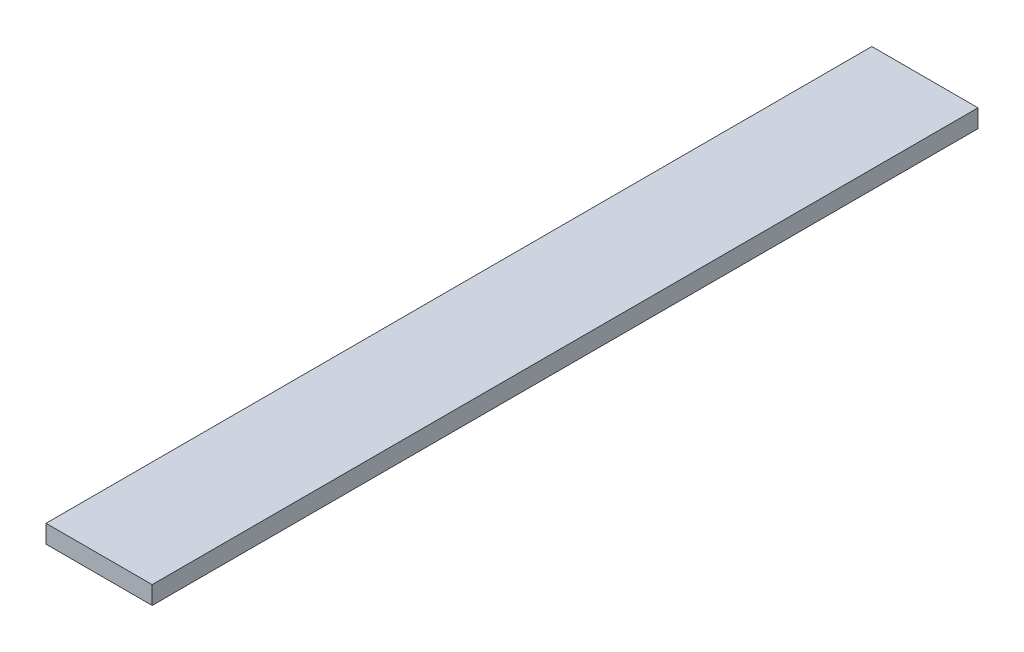
SolidWorks part; units mm, degrees
material "ABS"
ref_plane "Alzado" through (0, 0, 0) normal (0, 0, 1) x (1, 0, 0)
ref_plane "Planta" through (0, 0, 0) normal (0, 1, 0) x (1, 0, 0)
ref_plane "Vista lateral" through (0, 0, 0) normal (1, 0, 0) x (0, 0, -1)
sketch "Croquis1" plane through (0, 0, 0) normal (0, 0, 1) x (1, 0, 0)
  line L1 (0, 0) -> (135, 0)
  line L2 (0, 0) -> (0, 23)
  line L3 (0, 23) -> (135, 23)
  line L4 (135, 0) -> (135, 23)
  dimension "D1" = 135
  dimension "D2" = 23
extrude "Saliente-Extruir1" add sketch "Croquis1" against normal blind 1050
